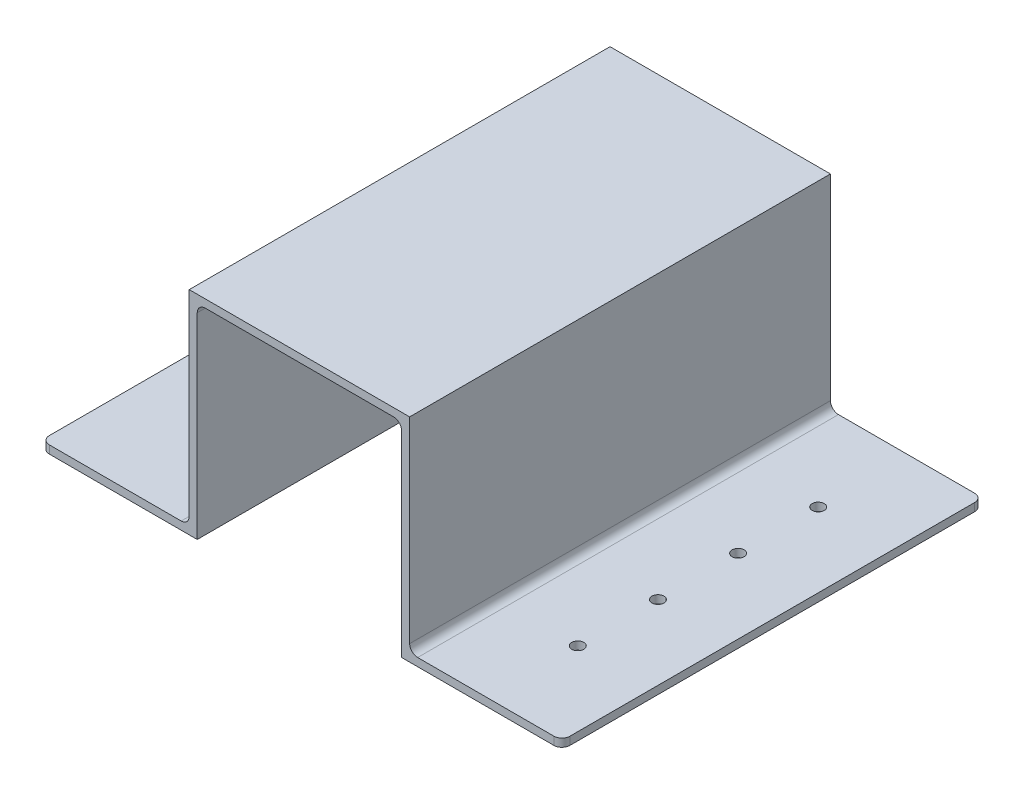
SolidWorks part; units mm, degrees
ref_plane "Front Plane" through (0, 0, 0) normal (0, 0, 1) x (1, 0, 0)
ref_plane "Top Plane" through (0, 0, 0) normal (0, 1, 0) x (1, 0, 0)
ref_plane "Right Plane" through (0, 0, 0) normal (1, 0, 0) x (0, 0, -1)
sketch "Sketch1" plane through (0, 0, 0) normal (0, 0, 1) x (1, 0, 0)
  line L0 (-42.0848, 1.4261) -> (8.9152, 1.4261)
  line L1 (8.9152, 1.4261) -> (8.9152, -49.5739)
  line L2 (-42.0848, 1.4261) -> (-42.0848, -49.5739)
  line L3 (8.9152, -49.5739) -> (48.9152, -49.5739)
  line L4 (-42.0848, -49.5739) -> (-80.9995, -49.5739)
  line L5 (-80.9995, -49.5739) -> (-80.9995, -47.5739)
  line L6 (-80.9995, -47.5739) -> (-44.0848, -47.5739)
  line L7 (-44.0848, -47.5739) -> (-44.0848, 3.4261)
  line L8 (-44.0848, 3.4261) -> (10.9152, 3.4261)
  line L9 (10.9152, 3.4261) -> (10.9152, -47.5739)
  line L10 (10.9152, -47.5739) -> (48.9152, -47.5739)
  line L11 (48.9152, -47.5739) -> (48.9152, -49.5739)
extrude "Boss-Extrude1" add sketch "Sketch1" along normal blind 105
fillet "Fillet2" radius 2 1 edges at (-44.0848, -47.5739, 52.5)
fillet "Fillet3" radius 2 1 edges at (-42.0848, 1.4261, 52.5)
fillet "Fillet4" radius 2 1 edges at (8.9152, 1.4261, 52.5)
fillet "Fillet5" radius 2 1 edges at (10.9152, -47.5739, 52.5)
sketch "Sketch2" plane through (0, -47.5739, 0) normal (0, 1, 0) x (1, 0, 0)
  circle A0 centre (-63.5421, -42.5) radius 1.5
  circle A1 centre (-63.5421, -22.5) radius 1.5
  circle A2 centre (-63.5421, -82.5) radius 1.5
  circle A3 centre (-63.5421, -62.5) radius 1.5
  circle A4 centre (30.3726, -82.5) radius 1.5
  circle A5 centre (30.3726, -62.5) radius 1.5
  circle A6 centre (30.3726, -42.5) radius 1.5
  circle A7 centre (30.3726, -22.5) radius 1.5
extrude "Cut-Extrude1" cut sketch "Sketch2" against normal blind 105
fillet "Fillet6" radius 2 4 edges at (48.9152, -48.5739, 105) (-80.9995, -48.5739, 105) (-80.9995, -48.5739, 0) (48.9152, -48.5739, 0)
